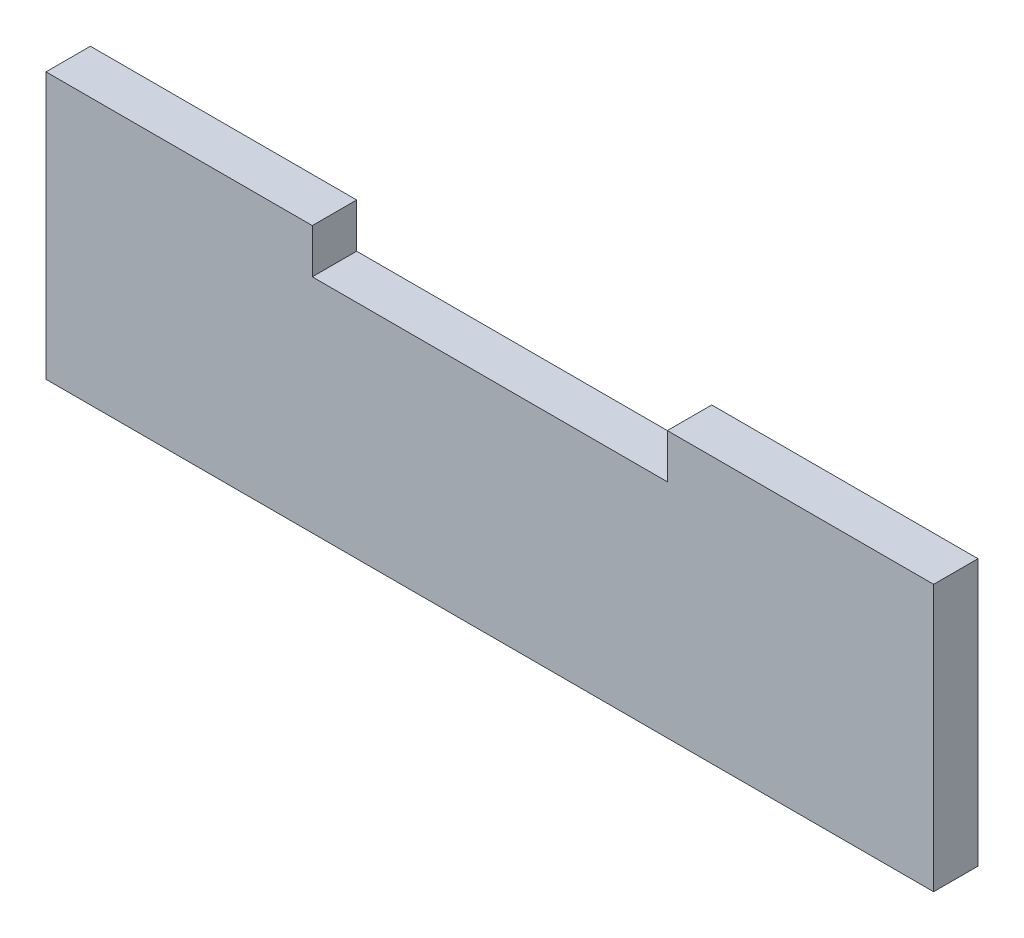
SolidWorks part; units mm, degrees
ref_plane "Front Plane" through (0, 0, 0) normal (0, 0, 1) x (1, 0, 0)
ref_plane "Top Plane" through (0, 0, 0) normal (0, 1, 0) x (1, 0, 0)
ref_plane "Right Plane" through (0, 0, 0) normal (1, 0, 0) x (0, 0, -1)
sketch "Sketch1" plane through (0, 0, 0) normal (0, 0, 1) x (1, 0, 0)
  line L0 (0, -21.3627) -> (0, 46.1737) construction
  line L1 (-50, -15) -> (50, -15)
  line L2 (-50, -15) -> (-50, 15)
  line L3 (-50, 15) -> (-20, 15)
  line L4 (50, -15) -> (50, 15)
  line L5 (-50, -15) -> (50, 15) construction
  line L6 (-50, 15) -> (50, -15) construction
  line L7 (-35, 3.3271) -> (-35, -23.9447) construction
  line L8 (-20, 15) -> (-20, 10)
  line L9 (-20, 10) -> (20, 10)
  line L10 (20, 15) -> (50, 15)
  line L11 (20, 10) -> (20, 15)
  point P0 (0, 0)
  point P8 (20, -21.3627)
  point P9 (20, 46.1737)
  point P10 (-20, -21.3627)
  point P11 (-20, 46.1737)
  dimension "D1" = 30
  dimension "D2" = 100
  dimension "D3" = 35
  dimension "D5" = 20
  dimension "D4" = 5
  dimension "D6" = 20
extrude "Boss-Extrude1" add sketch "Sketch1" along normal blind 5
